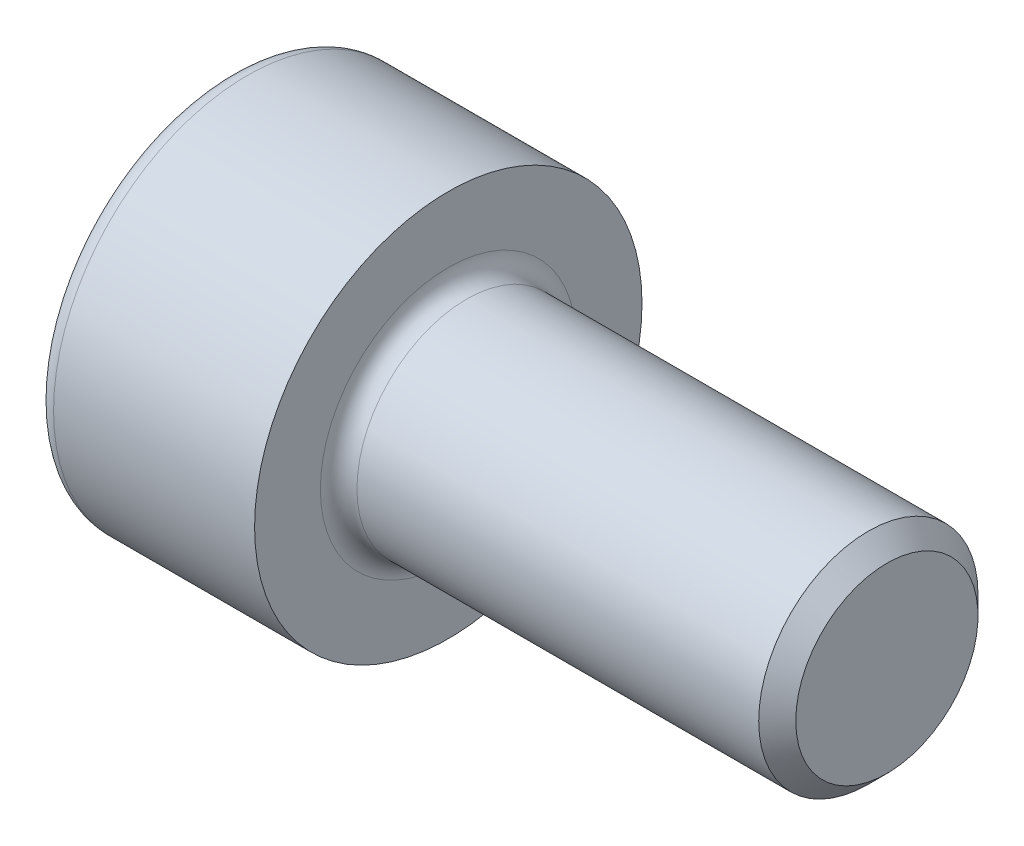
SolidWorks part; units mm, degrees
ref_plane "Front" through (0, 0, 0) normal (0, 0, 1) x (1, 0, 0)
ref_plane "Top" through (0, 0, 0) normal (0, 1, 0) x (1, 0, 0)
ref_plane "Right" through (0, 0, 0) normal (1, 0, 0) x (0, 0, -1)
sketch "Sketch1" plane through (0, 0, 0) normal (0, 0, 1) x (1, 0, 0)
  line L0 (5.7465, 1.5) -> (0.25, 1.5)
  line L1 (-3, 2.4) -> (-3, 0)
  line L2 (0, 2.65) -> (-2.75, 2.65)
  line L3 (0, 1.75) -> (0, 2.65)
  line L4 (6, 1.2465) -> (6, 0)
  line L5 (6, 1.2465) -> (5.7465, 1.5)
  line L6 (-3, 0) -> (0, 0) construction
  line L7 (-3, 0) -> (6, 0)
  arc A0 (-2.75, 2.65) -> (-3, 2.4) centre (-2.75, 2.4) ccw
  arc A1 (0, 1.75) -> (0.25, 1.5) centre (0.25, 1.75) ccw
  point P12 (0, 2.2)
  dimension "D5" = 0.25
  dimension "D1" = 3
  dimension "D2" = 5.3
  dimension "D3" = 135
  dimension "D4" = 0.3585
  dimension "D6" = 6
  dimension "D7" = 3
revolve "Revolve1" add sketch "Sketch1" angle 360 about L7
sketch "Sketch2" plane through (-3, 0, 0) normal (-1, 0, 0) x (0, 0, 1)
  line L7 (0.75, 0.433) -> (0, 0.866)
  line L8 (0, 0.866) -> (-0.75, 0.433)
  line L9 (-0.75, 0.433) -> (-0.75, -0.433)
  line L10 (-0.75, -0.433) -> (0, -0.866)
  line L11 (0, -0.866) -> (0.75, -0.433)
  line L12 (0.75, -0.433) -> (0.75, 0.433)
  circle A0 centre (0, 0) radius 0.75 construction
  dimension "D1" = 1.5
extrude "Cut-Extrude1" cut sketch "Sketch2" against normal blind 1.1
